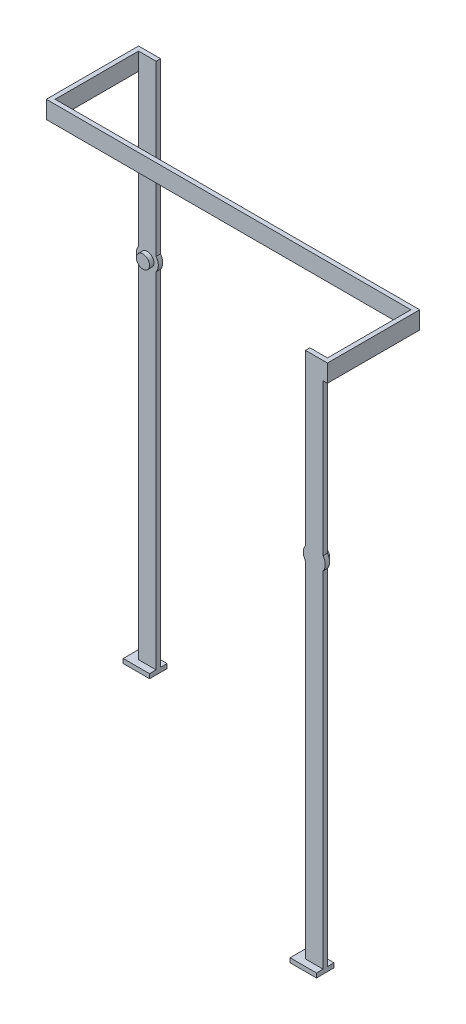
SolidWorks part; units mm, degrees
ref_plane "前视基准面" through (0, 0, 0) normal (0, 0, 1) x (1, 0, 0)
ref_plane "上视基准面" through (0, 0, 0) normal (0, 1, 0) x (1, 0, 0)
ref_plane "右视基准面" through (0, 0, 0) normal (1, 0, 0) x (0, 0, -1)
sketch "草图1" plane through (0, 0, 19.5) normal (0, 0, 1) x (1, 0, 0)
  line L0 (56.6488, 85.1534) -> (60.6488, 85.1534)
  line L1 (60.6488, 43.6534) -> (60.6488, -34.8466)
  line L2 (56.6488, 85.1534) -> (56.6488, 46.6534)
  line L3 (56.6488, -34.8466) -> (60.6488, -34.8466)
  line L4 (60.6488, 85.1534) -> (60.6488, 46.6534)
  line L5 (56.6488, 43.6534) -> (56.6488, -34.8466)
  arc A0 (60.6488, 43.6534) -> (60.6488, 46.6534) centre (58.6488, 45.1534) ccw
  arc A1 (56.6488, 46.6534) -> (56.6488, 43.6534) centre (58.6488, 45.1534) ccw
  point P0 (58.6488, 45.1534)
  dimension "D1" = 40
  dimension "D2" = 80
extrude "凸台-拉伸2" add sketch "草图1" along normal blind 1
sketch "草图2" plane through (0, 0, 19.5) normal (0, 0, -1) x (-1, 0, 0)
  circle A0 centre (-58.6488, 45.1534) radius 1.5
extrude "凸台-拉伸3" add sketch "草图2" along normal blind 1
sketch "草图3" plane through (0, 0, -19.5) normal (0, 0, -1) x (-1, 0, 0)
  line L0 (17.3512, 43.6534) -> (17.3512, -34.8466)
  line L1 (17.3512, 85.1534) -> (21.3512, 85.1534)
  line L2 (17.3512, 85.1534) -> (17.3512, 46.6534)
  line L3 (17.3512, -34.8466) -> (21.3512, -34.8466)
  line L4 (21.3512, 85.1534) -> (21.3512, 46.6534)
  line L7 (21.3512, 43.6534) -> (21.3512, -34.8466)
  arc A0 (17.3512, 46.6534) -> (17.3512, 43.6534) centre (19.3512, 45.1534) ccw
  arc A1 (21.3512, 43.6534) -> (21.3512, 46.6534) centre (19.3512, 45.1534) ccw
  point P0 (19.3512, 45.1534)
  dimension "D1" = 4
  dimension "D2" = 80
  dimension "D3" = 40
extrude "凸台-拉伸4" add sketch "草图3" along normal blind 1 separate body
sketch "草图4" plane through (0, 0, -19.5) normal (0, 0, 1) x (1, 0, 0)
  circle A0 centre (-19.3512, 45.1534) radius 1.5
extrude "凸台-拉伸5" add sketch "草图4" along normal blind 1
sketch "草图5" plane through (0, 0, 0) normal (0, 0, 1) x (1, 0, 0)
  line L0 (60.6488, 46.6534) -> (60.6488, 85.1534) construction
  line L1 (-21.3512, 85.1534) -> (60.6488, 85.1534)
  line L2 (-21.3512, 85.1534) -> (-21.3512, 81.1534)
  line L3 (-21.3512, 81.1534) -> (60.6488, 81.1534)
  line L4 (60.6488, 85.1534) -> (60.6488, 81.1534)
  dimension "D1" = 4
extrude "凸台-拉伸6" add sketch "草图5" along normal mid plane 1 separate body
sketch "草图6" plane through (60.6488, 0, 0) normal (1, 0, 0) x (0, 0, -1)
  line L1 (-20.5, 85.1534) -> (0.5, 85.1534)
  line L2 (-20.5, 85.1534) -> (-20.5, 81.1534)
  line L3 (-20.5, 81.1534) -> (0.5, 81.1534)
  line L4 (0.5, 85.1534) -> (0.5, 81.1534)
extrude "凸台-拉伸7" add sketch "草图6" along normal blind 1
sketch "草图7" plane through (-21.3512, 0, 0) normal (-1, 0, 0) x (0, 0, 1)
  line L1 (-20.5, 85.1534) -> (0.5, 85.1534)
  line L2 (-20.5, 85.1534) -> (-20.5, 81.1534)
  line L3 (-20.5, 81.1534) -> (0.5, 81.1534)
  line L4 (0.5, 85.1534) -> (0.5, 81.1534)
extrude "凸台-拉伸8" add sketch "草图7" along normal blind 1
sketch "草图8" plane through (0, -34.8466, 0) normal (0, -1, 0) x (1, 0, 0)
  line L0 (-17.3512, -20.5) -> (-17.3512, -19.5) construction
  line L1 (-17.3512, -22) -> (-23.3512, -22)
  line L2 (-17.3512, -22) -> (-17.3512, -18)
  line L3 (-17.3512, -18) -> (-23.3512, -18)
  line L4 (-23.3512, -22) -> (-23.3512, -18)
  line L5 (-17.3512, -20.5) -> (-21.3512, -20.5) construction
  line L6 (-17.3512, -19.5) -> (-21.3512, -19.5) construction
  line L7 (-21.3512, -20.5) -> (-21.3512, -19.5) construction
  dimension "D1" = 0
  dimension "D2" = 1.5
  dimension "D3" = 1.5
  dimension "D4" = 2
extrude "凸台-拉伸9" add sketch "草图8" along normal blind 1
sketch "草图9" plane through (0, -34.8466, 0) normal (0, -1, 0) x (1, 0, 0)
  line L0 (60.6488, 20.5) -> (60.6488, 19.5) construction
  line L1 (54.6488, 22) -> (60.6488, 22)
  line L2 (54.6488, 22) -> (54.6488, 18)
  line L3 (54.6488, 18) -> (60.6488, 18)
  line L4 (60.6488, 22) -> (60.6488, 18)
  line L5 (56.6488, 20.5) -> (60.6488, 20.5) construction
  line L6 (56.6488, 19.5) -> (60.6488, 19.5) construction
  line L7 (56.6488, 20.5) -> (56.6488, 19.5) construction
  dimension "D1" = 0
  dimension "D2" = 1.5
  dimension "D3" = 1.5
  dimension "D4" = 2
extrude "凸台-拉伸10" add sketch "草图9" along normal blind 1
